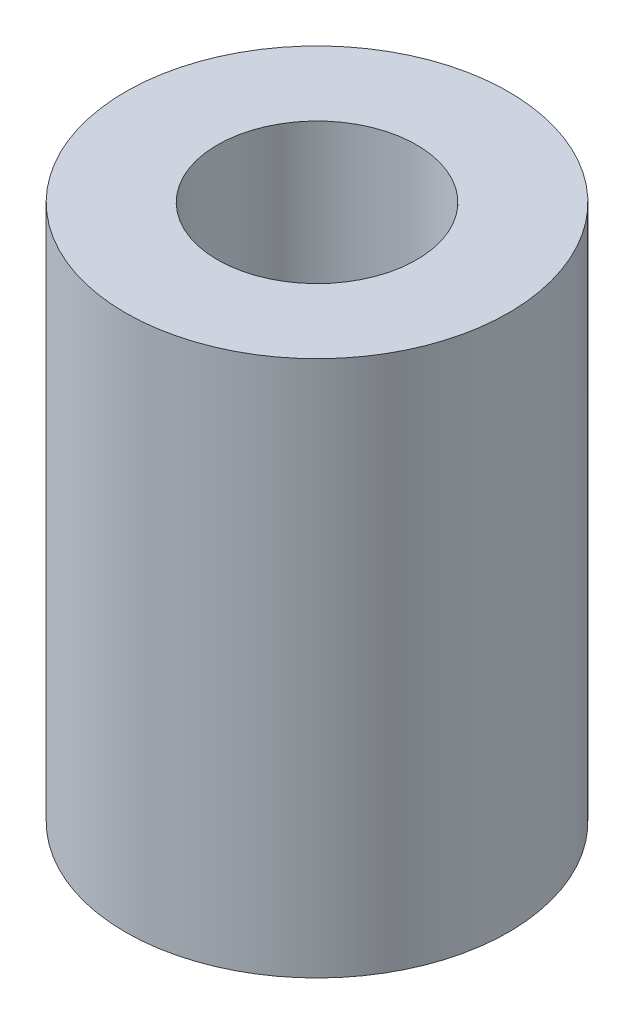
SolidWorks part; units mm, degrees
ref_plane "Front" through (0, 0, 0) normal (0, 0, 1) x (1, 0, 0)
ref_plane "Top" through (0, 0, 0) normal (0, 1, 0) x (1, 0, 0)
ref_plane "Right" through (0, 0, 0) normal (1, 0, 0) x (0, 0, -1)
sketch "Sketch1" plane through (0, 0, 0) normal (0, 1, 0) x (1, 0, 0)
  circle A0 centre (0, 0) radius 2.6
  circle A1 centre (0, 0) radius 5
  dimension "D1" = 5.2
  dimension "D2" = 10
extrude "Boss-Extrude1" add sketch "Sketch1" along normal blind 14
